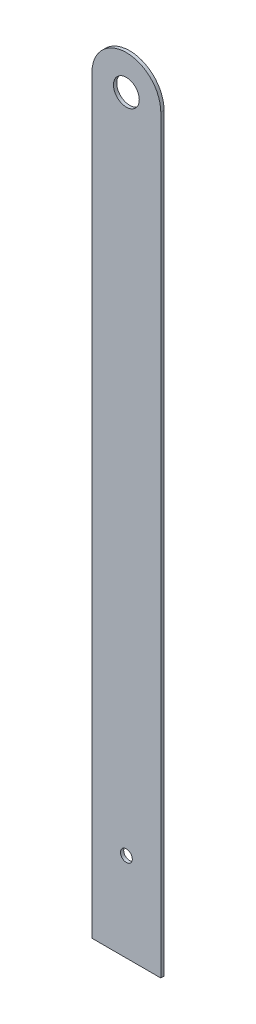
SolidWorks part; units mm, degrees
material "Alloy Steel"
ref_plane "Front" through (0, 0, 0) normal (0, 0, 1) x (1, 0, 0)
ref_plane "Top" through (0, 0, 0) normal (0, 1, 0) x (1, 0, 0)
ref_plane "Right" through (0, 0, 0) normal (1, 0, 0) x (0, 0, -1)
sketch "Sketch1" plane through (0, 0, 0) normal (0, 0, 1) x (1, 0, 0)
  line L1 (-12.7, 138.43) -> (12.7, 138.43)
  line L2 (-12.7, 138.43) -> (-12.7, -138.43)
  line L3 (-12.7, -138.43) -> (12.7, -138.43)
  line L4 (12.7, 138.43) -> (12.7, -138.43)
  line L5 (-12.7, 138.43) -> (12.7, -138.43) construction
  line L6 (-12.7, -138.43) -> (12.7, 138.43) construction
  arc A0 (-12.7, 138.43) -> (12.7, 138.43) centre (0, 138.43) cw
  point P0 (0, 0)
  dimension "D3" = 12.7
  dimension "D1" = 276.86
  dimension "D2" = 25.4
extrude "Boss-Extrude1" add sketch "Sketch1" along normal blind 1.2 contours L4 L1 L2 L3 | A0 L1
sketch "Sketch2" plane through (0, 0, 1.2) normal (0, 0, 1) x (1, 0, 0)
  circle A0 centre (0, 138.43) radius 4.7625
  dimension "D1" = 9.525
extrude "Cut-Extrude1" cut sketch "Sketch2" against normal through all
sketch "Sketch3" plane through (0, 0, 1.2) normal (0, 0, 1) x (1, 0, 0)
  line L0 (-12.7, -138.43) -> (12.7, -138.43) construction
  circle A0 centre (0, -105.6686) radius 2.1828
  dimension "D1" = 32.7614
  dimension "D2" = 4.3656
extrude "Cut-Extrude2" cut sketch "Sketch3" against normal through all
